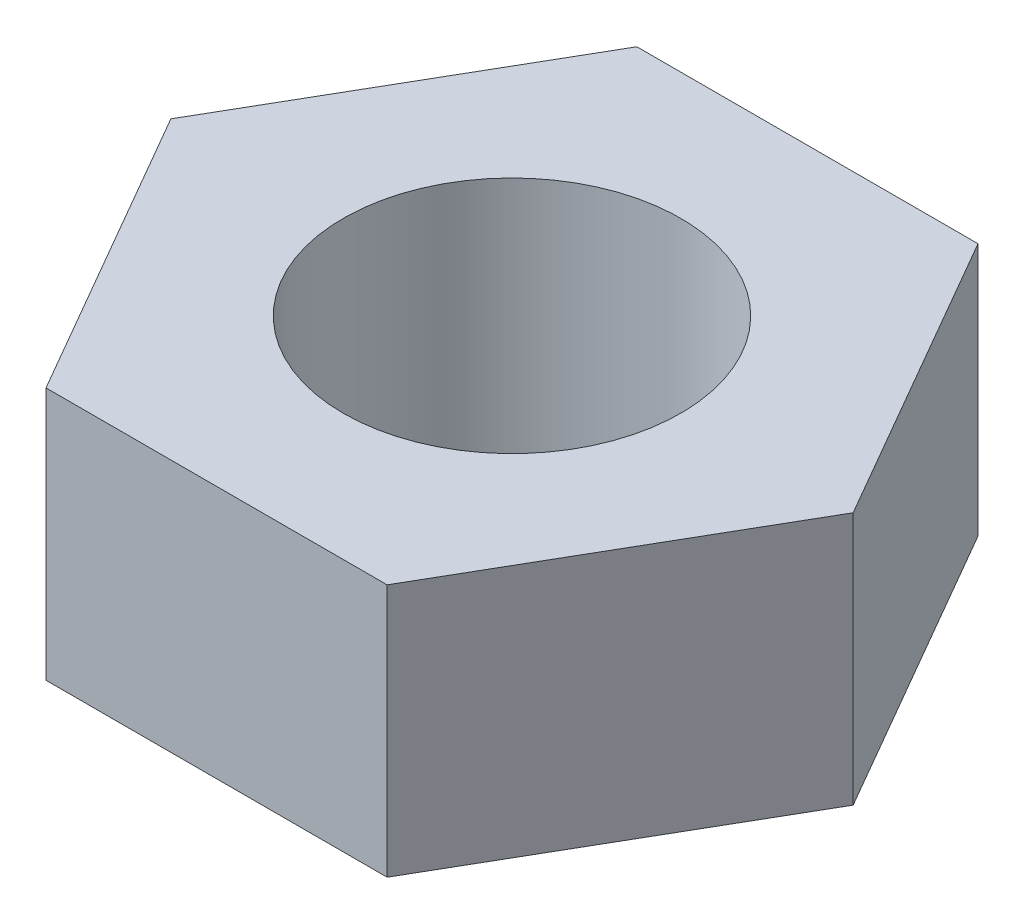
SolidWorks part; units mm, degrees
ref_plane "前视基准面" through (0, 0, 0) normal (0, 0, 1) x (1, 0, 0)
ref_plane "上视基准面" through (0, 0, 0) normal (0, 1, 0) x (1, 0, 0)
ref_plane "右视基准面" through (0, 0, 0) normal (1, 0, 0) x (0, 0, -1)
sketch "草图1" plane through (0, 0, 0) normal (0, 1, 0) x (1, 0, 0)
  line L1 (4.0415, 0) -> (2.0207, 3.5)
  line L2 (2.0207, 3.5) -> (-2.0207, 3.5)
  line L3 (-2.0207, 3.5) -> (-4.0415, 0)
  line L4 (-4.0415, 0) -> (-2.0207, -3.5)
  line L5 (-2.0207, -3.5) -> (2.0207, -3.5)
  line L6 (2.0207, -3.5) -> (4.0415, 0)
  circle A0 centre (0, 0) radius 3.5 construction
  circle A1 centre (0, 0) radius 2
extrude "凸台-拉伸1" add sketch "草图1" along normal blind 3
